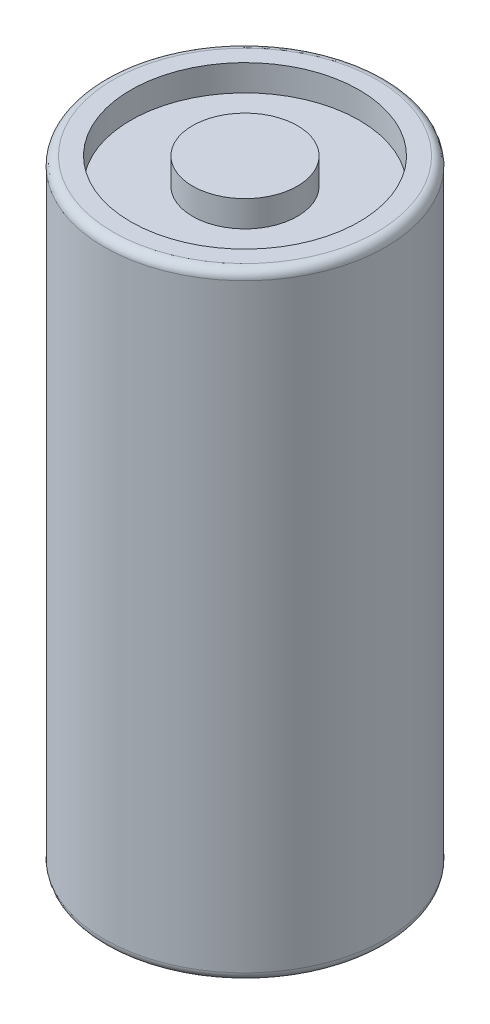
SolidWorks part; units mm, degrees
ref_plane "前视基准面" through (0, 0, 0) normal (0, 0, 1) x (1, 0, 0)
ref_plane "上视基准面" through (0, 0, 0) normal (0, 1, 0) x (1, 0, 0)
ref_plane "右视基准面" through (0, 0, 0) normal (1, 0, 0) x (0, 0, -1)
sketch "草图1" plane through (0, 0, 0) normal (0, 1, 0) x (1, 0, 0)
  circle A0 centre (0, 0) radius 16.1
  dimension "D1" = 32.2
extrude "凸台-拉伸1" add sketch "草图1" along normal blind 70.6
sketch "草图3" plane through (0, 70.6, 0) normal (0, 1, 0) x (1, 0, 0)
  circle A0 centre (0, 0) radius 6
  circle A1 centre (0, 0) radius 13.0738
  dimension "D1" = 12
extrude "切除-拉伸1" cut sketch "草图3" against normal blind 3
fillet "圆角1" radius 1 1 edges at (0, 0, 16.1)
fillet "圆角2" radius 1 1 edges at (0, 70.6, 16.1)
ref_plane "基准面1" through (-16.1, 0, 0) normal (-1, 0, 0) x (0, 0, 1)
